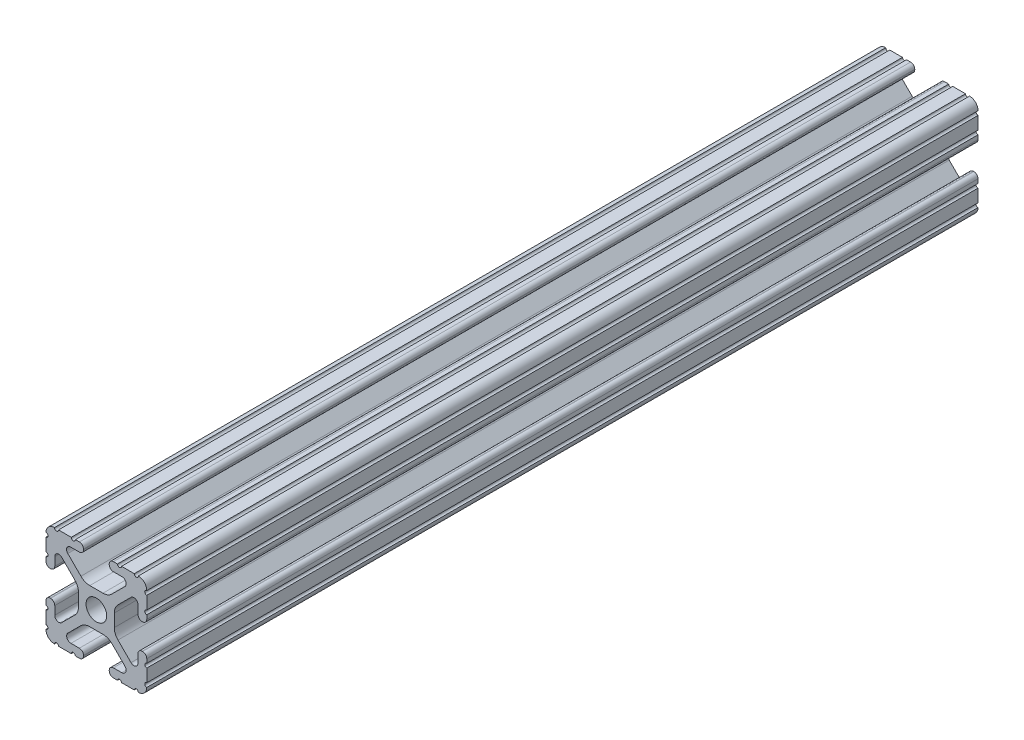
SolidWorks part; units mm, degrees
ref_plane "Front Plane" through (0, 0, 0) normal (0, 0, 1) x (1, 0, 0)
ref_plane "Top Plane" through (0, 0, 0) normal (0, 1, 0) x (1, 0, 0)
ref_plane "Right Plane" through (0, 0, 0) normal (1, 0, 0) x (0, 0, -1)
sketch "Sketch1" plane through (0, 0, 0) normal (0, 0, 1) x (1, 0, 0)
  line L88 (-7.1797, -8.6452) -> (-3.9523, -5.4237)
  line L89 (-1.7093, -4.4958) -> (1.7093, -4.4958)
  line L90 (3.9523, -5.4237) -> (7.1797, -8.6452)
  line L91 (6.4164, -10.4902) -> (4.2875, -10.4902)
  line L92 (3.2385, -11.5392) -> (3.2385, -11.651)
  line L93 (4.2875, -12.7) -> (5.3171, -12.7)
  line L94 (6.3331, -12.7) -> (9.5504, -12.7)
  line L95 (12.7, -9.5504) -> (12.7, -6.3331)
  line L96 (12.7, -5.3171) -> (12.7, -4.2875)
  line L97 (11.651, -3.2385) -> (11.5392, -3.2385)
  line L98 (10.4902, -4.2875) -> (10.4902, -6.4021)
  line L99 (8.7371, -7.1294) -> (5.441, -3.8408)
  line L100 (4.5085, -1.5932) -> (4.5085, 1.5932)
  line L101 (5.441, 3.8408) -> (8.7371, 7.1294)
  line L102 (10.4902, 6.4021) -> (10.4902, 4.2875)
  line L103 (11.5392, 3.2385) -> (11.651, 3.2385)
  line L104 (12.7, 4.2875) -> (12.7, 5.3171)
  line L105 (12.7, 6.3331) -> (12.7, 9.5504)
  line L106 (9.5504, 12.7) -> (6.3331, 12.7)
  line L107 (5.3171, 12.7) -> (4.2875, 12.7)
  line L108 (3.2385, 11.651) -> (3.2385, 11.5392)
  line L109 (4.2875, 10.4902) -> (6.4768, 10.4902)
  line L110 (7.207, 8.7244) -> (3.8983, 5.4232)
  line L111 (1.6558, 4.4958) -> (-1.6558, 4.4958)
  line L112 (-3.8983, 5.4232) -> (-7.207, 8.7244)
  line L113 (-6.4768, 10.4902) -> (-4.2875, 10.4902)
  line L114 (-3.2385, 11.5392) -> (-3.2385, 11.651)
  line L115 (-4.2875, 12.7) -> (-5.3171, 12.7)
  line L116 (-6.3331, 12.7) -> (-9.5504, 12.7)
  line L117 (-12.7, 9.5504) -> (-12.7, 6.3331)
  line L118 (-12.7, 5.3171) -> (-12.7, 4.2875)
  line L119 (-11.651, 3.2385) -> (-11.5392, 3.2385)
  line L120 (-10.4902, 4.2875) -> (-10.4902, 6.4021)
  line L121 (-8.7371, 7.1294) -> (-5.441, 3.8408)
  line L122 (-4.5085, 1.5932) -> (-4.5085, -1.5932)
  line L123 (-5.441, -3.8408) -> (-8.7371, -7.1294)
  line L124 (-10.4902, -6.4021) -> (-10.4902, -4.2875)
  line L125 (-11.5392, -3.2385) -> (-11.651, -3.2385)
  line L126 (-12.7, -4.2875) -> (-12.7, -5.3171)
  line L127 (-12.7, -6.3331) -> (-12.7, -9.5504)
  line L128 (-9.5504, -12.7) -> (-6.3331, -12.7)
  line L129 (-5.3171, -12.7) -> (-4.2875, -12.7)
  line L130 (-3.2385, -11.651) -> (-3.2385, -11.5392)
  line L131 (-4.2875, -10.4902) -> (-6.4164, -10.4902)
  circle A1 centre (0, 0) radius 2.6035
  arc A104 (-7.1797, -8.6452) -> (-6.4164, -10.4902) centre (-6.4164, -9.4098) ccw
  arc A105 (-1.7093, -4.4958) -> (-3.9523, -5.4237) centre (-1.7093, -7.6708) ccw
  arc A106 (3.9523, -5.4237) -> (1.7093, -4.4958) centre (1.7093, -7.6708) ccw
  arc A107 (6.4164, -10.4902) -> (7.1797, -8.6452) centre (6.4164, -9.4098) ccw
  arc A108 (4.2875, -10.4902) -> (3.2385, -11.5392) centre (4.2875, -11.5392) ccw
  arc A109 (3.2385, -11.651) -> (4.2875, -12.7) centre (4.2875, -11.651) ccw
  arc A110 (6.3331, -12.7) -> (5.3171, -12.7) centre (5.8251, -12.7) ccw
  arc A111 (10.5664, -12.6998) -> (9.5504, -12.7) centre (10.0584, -12.7) ccw
  arc A112 (10.5664, -12.6998) -> (12.6998, -10.5664) centre (10.5918, -10.5918) ccw
  arc A113 (12.7, -9.5504) -> (12.6998, -10.5664) centre (12.7, -10.0584) ccw
  arc A114 (12.7, -5.3171) -> (12.7, -6.3331) centre (12.7, -5.8251) ccw
  arc A115 (12.7, -4.2875) -> (11.651, -3.2385) centre (11.651, -4.2875) ccw
  arc A116 (11.5392, -3.2385) -> (10.4902, -4.2875) centre (11.5392, -4.2875) ccw
  arc A117 (8.7371, -7.1294) -> (10.4902, -6.4021) centre (9.4628, -6.4021) ccw
  arc A118 (4.5085, -1.5932) -> (5.441, -3.8408) centre (7.6835, -1.5932) ccw
  arc A119 (5.441, 3.8408) -> (4.5085, 1.5932) centre (7.6835, 1.5932) ccw
  arc A120 (10.4902, 6.4021) -> (8.7371, 7.1294) centre (9.4628, 6.4021) ccw
  arc A121 (10.4902, 4.2875) -> (11.5392, 3.2385) centre (11.5392, 4.2875) ccw
  arc A122 (11.651, 3.2385) -> (12.7, 4.2875) centre (11.651, 4.2875) ccw
  arc A123 (12.7, 6.3331) -> (12.7, 5.3171) centre (12.7, 5.8251) ccw
  arc A124 (12.6998, 10.5664) -> (12.7, 9.5504) centre (12.7, 10.0584) ccw
  arc A125 (12.6998, 10.5664) -> (10.5664, 12.6998) centre (10.5918, 10.5918) ccw
  arc A126 (9.5504, 12.7) -> (10.5664, 12.6998) centre (10.0584, 12.7) ccw
  arc A127 (5.3171, 12.7) -> (6.3331, 12.7) centre (5.8251, 12.7) ccw
  arc A128 (4.2875, 12.7) -> (3.2385, 11.651) centre (4.2875, 11.651) ccw
  arc A129 (3.2385, 11.5392) -> (4.2875, 10.4902) centre (4.2875, 11.5392) ccw
  arc A130 (7.207, 8.7244) -> (6.4768, 10.4902) centre (6.4768, 9.4563) ccw
  arc A131 (1.6558, 4.4958) -> (3.8983, 5.4232) centre (1.6558, 7.6708) ccw
  arc A132 (-3.8983, 5.4232) -> (-1.6558, 4.4958) centre (-1.6558, 7.6708) ccw
  arc A133 (-6.4768, 10.4902) -> (-7.207, 8.7244) centre (-6.4768, 9.4563) ccw
  arc A134 (-4.2875, 10.4902) -> (-3.2385, 11.5392) centre (-4.2875, 11.5392) ccw
  arc A135 (-3.2385, 11.651) -> (-4.2875, 12.7) centre (-4.2875, 11.651) ccw
  arc A136 (-6.3331, 12.7) -> (-5.3171, 12.7) centre (-5.8251, 12.7) ccw
  arc A137 (-10.5664, 12.6998) -> (-9.5504, 12.7) centre (-10.0584, 12.7) ccw
  arc A138 (-10.5664, 12.6998) -> (-12.6998, 10.5664) centre (-10.5918, 10.5918) ccw
  arc A139 (-12.7, 9.5504) -> (-12.6998, 10.5664) centre (-12.7, 10.0584) ccw
  arc A140 (-12.7, 5.3171) -> (-12.7, 6.3331) centre (-12.7, 5.8251) ccw
  arc A141 (-12.7, 4.2875) -> (-11.651, 3.2385) centre (-11.651, 4.2875) ccw
  arc A142 (-11.5392, 3.2385) -> (-10.4902, 4.2875) centre (-11.5392, 4.2875) ccw
  arc A143 (-8.7371, 7.1294) -> (-10.4902, 6.4021) centre (-9.4628, 6.4021) ccw
  arc A144 (-4.5085, 1.5932) -> (-5.441, 3.8408) centre (-7.6835, 1.5932) ccw
  arc A145 (-5.441, -3.8408) -> (-4.5085, -1.5932) centre (-7.6835, -1.5932) ccw
  arc A146 (-10.4902, -6.4021) -> (-8.7371, -7.1294) centre (-9.4628, -6.4021) ccw
  arc A147 (-10.4902, -4.2875) -> (-11.5392, -3.2385) centre (-11.5392, -4.2875) ccw
  arc A148 (-11.651, -3.2385) -> (-12.7, -4.2875) centre (-11.651, -4.2875) ccw
  arc A149 (-12.7, -6.3331) -> (-12.7, -5.3171) centre (-12.7, -5.8251) ccw
  arc A150 (-12.6998, -10.5664) -> (-12.7, -9.5504) centre (-12.7, -10.0584) ccw
  arc A151 (-12.6998, -10.5664) -> (-10.5664, -12.6998) centre (-10.5918, -10.5918) ccw
  arc A152 (-9.5504, -12.7) -> (-10.5664, -12.6998) centre (-10.0584, -12.7) ccw
  arc A153 (-5.3171, -12.7) -> (-6.3331, -12.7) centre (-5.8251, -12.7) ccw
  arc A154 (-4.2875, -12.7) -> (-3.2385, -11.651) centre (-4.2875, -11.651) ccw
  arc A155 (-3.2385, -11.5392) -> (-4.2875, -10.4902) centre (-4.2875, -11.5392) ccw
extrude "Boss-Extrude1" add sketch "Sketch1" along normal mid plane 209.55
sketch "Sketch2" plane through (0, 4.4958, 0) normal (0, 1, 0) x (1, 0, 0)
  line L0 (1.6558, 104.775) -> (-1.6558, 104.775) construction
  circle A0 centre (0, 92.075) radius 3.175
  dimension "D1" = 12.7
  dimension "D2" = 6.35
extrude "Cut-Extrude1" cut sketch "Sketch2" against normal through all and the other way through all
